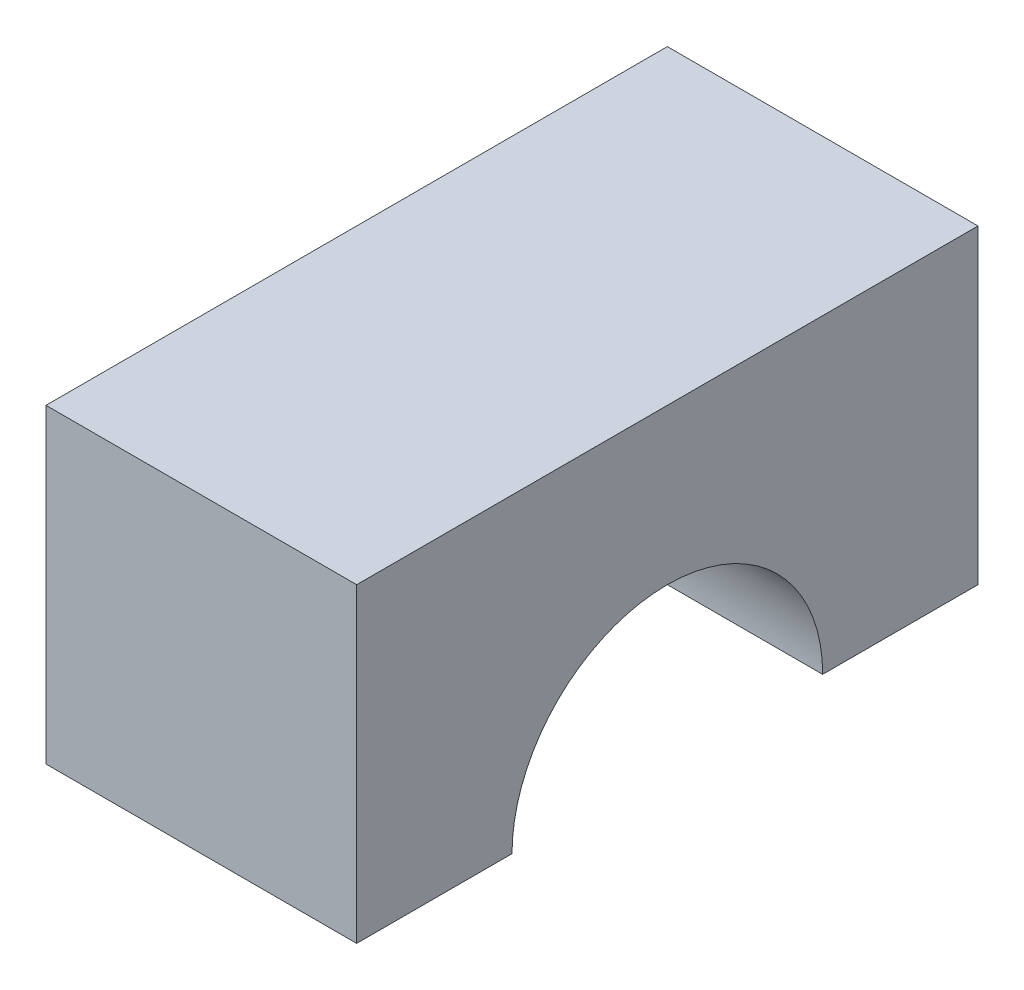
SolidWorks part; units mm, degrees
ref_plane "Front Plane" through (0, 0, 0) normal (0, 0, 1) x (1, 0, 0)
ref_plane "Top Plane" through (0, 0, 0) normal (0, 1, 0) x (1, 0, 0)
ref_plane "Right Plane" through (0, 0, 0) normal (1, 0, 0) x (0, 0, -1)
sketch "Sketch1" plane through (0, 0, 0) normal (1, 0, 0) x (0, 0, -1)
  line L1 (0, 0) -> (2.459, 0)
  line L2 (0, 0) -> (0, 25.4)
  line L3 (0, 25.4) -> (50.8, 25.4)
  line L4 (50.8, 0) -> (50.8, 25.4)
  line L5 (0, 0) -> (12.7, 0)
  line L6 (38.1, 0) -> (50.8, 0)
  arc A1 (38.1, 0) -> (12.7, 0) centre (25.4, 0) ccw
  dimension "D3" = 25.4
  dimension "D1" = 25.4
  dimension "D2" = 50.8
extrude "Boss-Extrude1" add sketch "Sketch1" along normal blind 25.4 contours A1 L6 L4 L3 L2 L1 L5
